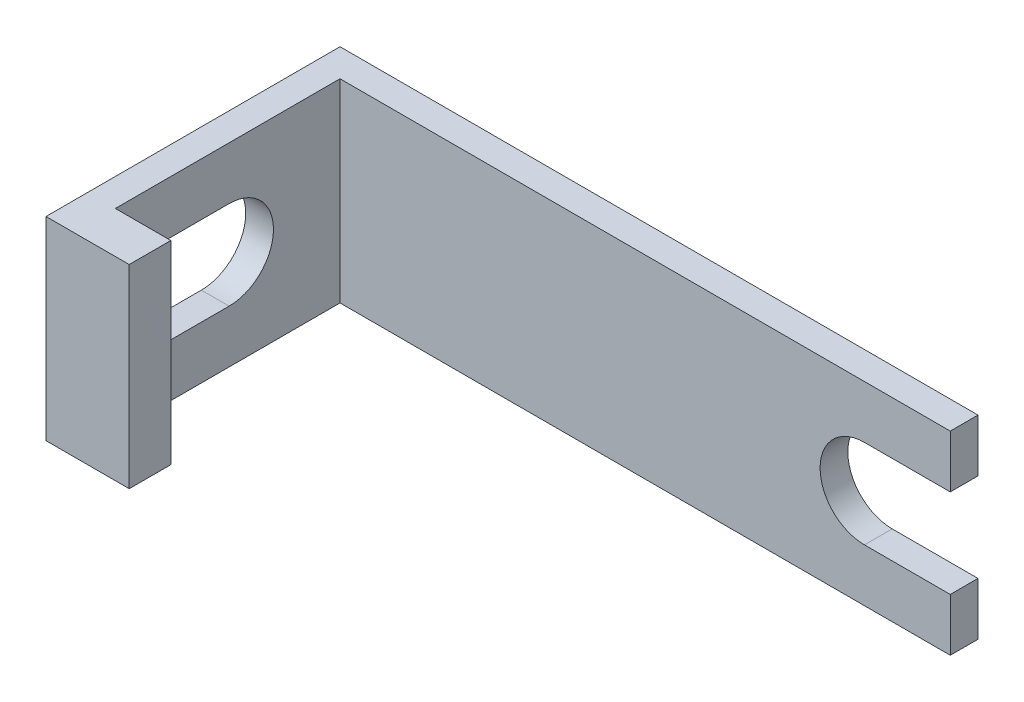
SolidWorks part; units mm, degrees
ref_plane "Płaszczyzna przednia" through (0, 0, 0) normal (0, 0, 1) x (1, 0, 0)
ref_plane "Płaszczyzna górna" through (0, 0, 0) normal (0, 1, 0) x (1, 0, 0)
ref_plane "Płaszczyzna prawa" through (0, 0, 0) normal (1, 0, 0) x (0, 0, -1)
sketch "Szkic1" plane through (0, 0, 0) normal (0, 0, 1) x (1, 0, 0)
  line L0 (-7.2066, 4.5226) -> (-7.2066, -2.4774)
  line L1 (-7.2066, -2.4774) -> (15.7934, -2.4774)
  line L2 (15.7934, 4.5226) -> (15.7934, 2.6226)
  line L3 (15.7934, 4.5226) -> (-7.2066, 4.5226)
  line L4 (-7.2066, -11.8363) -> (-7.2066, 11.1309) construction
  line L5 (13.6204, 2.6226) -> (15.7934, 2.6226)
  line L6 (13.6204, -0.5774) -> (15.7934, -0.5774)
  line L7 (13.6204, 1.0226) -> (5.0906, 1.0226) construction
  line L8 (13.6204, 2.6226) -> (12.7004, 2.6226)
  line L9 (13.6204, -0.5774) -> (12.7004, -0.5774)
  line L10 (15.7934, -0.5774) -> (15.7934, -2.4774)
  arc A2 (12.7004, 2.6226) -> (12.7004, -0.5774) centre (12.7004, 1.0226) ccw
  dimension "D1" = 23
extrude "Dodanie-wyciągnięcie1" add sketch "Szkic1" along normal blind 1
sketch "Szkic12" plane through (-7.2066, 0, 0) normal (-1, 0, 0) x (0, 0, 1)
  line L0 (0, 4.5226) -> (0, -2.4774)
  line L1 (0, -2.4774) -> (9.1, -2.4774)
  line L2 (9.1, -2.4774) -> (9.1, 4.5226)
  line L3 (0, 4.5226) -> (9.1, 4.5226)
  dimension "D1" = 9.1
extrude "Dodanie-wyciągnięcie2" add sketch "Szkic12" against normal blind 1
sketch "Szkic15" plane through (-7.2066, 0, 0) normal (-1, 0, 0) x (0, 0, 1)
  line L0 (9.1, -2.4774) -> (10.6, -2.4774)
  line L1 (9.1, -2.4774) -> (9.1, 4.5226)
  line L2 (9.1, 4.5226) -> (10.6, 4.5226)
  line L3 (10.6, -2.4774) -> (10.6, 4.5226)
  dimension "D1" = 1.5
extrude "Dodanie-wyciągnięcie3" add sketch "Szkic15" against normal blind 3
sketch "Szkic16" plane through (-6.2066, 0, 0) normal (1, 0, 0) x (0, 0, -1)
  line L0 (-9.1, 1.0226) -> (-1, 1.0226) construction
  line L1 (-9.1, -2.4774) -> (-9.1, 4.5226) construction
  line L2 (-1, 4.5226) -> (-1, -2.4774) construction
  line L3 (-3.4, -5.8976) -> (-3.4, 8.6566) construction
  line L4 (0, 4.5226) -> (0, -2.4774) construction
  line L5 (-5, -3.5274) -> (-5, 9.1364) construction
  line L6 (-7.5, -4.207) -> (-7.5, 8.4224) construction
  line L7 (-9.1, 4.5226) -> (-9.1, -2.4774) construction
  line L8 (-7.5, -0.5774) -> (-5, -0.5774)
  line L9 (-7.5, 2.6226) -> (-5, 2.6226)
  arc A0 (-5, -0.5774) -> (-5, 2.6226) centre (-5, 1.0226) ccw
  arc A1 (-7.5, 2.6226) -> (-7.5, -0.5774) centre (-7.5, 1.0226) ccw
  dimension "D1" = 3.4
  dimension "D2" = 1.6
  dimension "D3" = 1.6
extrude "Wytnij-wyciągnięcie1" cut sketch "Szkic16" against normal up to surface (1 mm away) up to face at (-7.2066, 1.0226, 5.3)
sketch "Linie zgięcia1" [suppressed] plane through (0, 0, 0) normal (0, 1, 0) x (1, 0, 0)
sketch "Ramka-graniczna1" [suppressed] plane through (0, 0, 0) normal (0, 1, 0) x (1, 0, 0)
